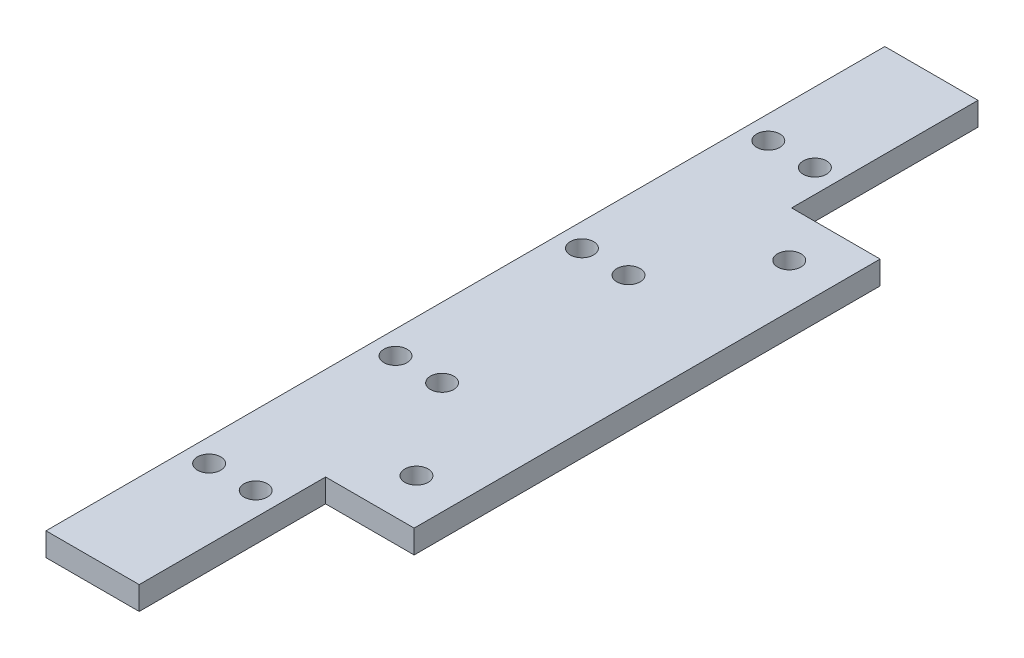
SolidWorks part; units mm, degrees
ref_plane "Front Plane" through (0, 0, 0) normal (0, 0, 1) x (1, 0, 0)
ref_plane "Top Plane" through (0, 0, 0) normal (0, 1, 0) x (1, 0, 0)
ref_plane "Right Plane" through (0, 0, 0) normal (1, 0, 0) x (0, 0, -1)
sketch "Sketch1" plane through (0, 0, 0) normal (0, 1, 0) x (1, 0, 0)
  line L1 (0, 0) -> (24.13, 0)
  line L2 (0, 0) -> (0, 127)
  line L3 (0, 127) -> (24.13, 127)
  line L4 (24.13, 0) -> (24.13, 127)
  dimension "D1" = 127
  dimension "D2" = 24.13
extrude "Boss-Extrude1" add sketch "Sketch1" along normal blind 6.35
sketch "Sketch3" plane through (0, 6.35, 0) normal (0, 1, 0) x (1, 0, 0)
  line L0 (12.065, 0) -> (12.065, 127)
  line L1 (0, 0) -> (24.13, 0) construction
  line L2 (24.13, 127) -> (0, 127) construction
  line L3 (12.065, 0) -> (12.065, 12.7)
  circle A0 centre (12.065, 12.7) radius 3.175
  circle A1 centre (12.065, 114.3) radius 3.175
  point P8 (12.065, 63.5)
  point P13 (12.065, 63.5)
  dimension "D2" = 6.35
  dimension "D1" = 12.7
  dimension "D3" = 2
extrude "Cut-Extrude2" cut sketch "Sketch3" against normal through all contours L0 A1 | L0 A1 | L3 A0 L0 | L0 A0 L3
sketch "Sketch5" plane through (0, 0, 0) normal (-1, 0, 0) x (0, 0, 1)
  line L1 (-127, 0) -> (0, 0)
  line L2 (-127, 0) -> (-127, 6.35)
  line L3 (-127, 6.35) -> (0, 6.35)
  line L4 (0, 0) -> (0, 6.35)
extrude "Boss-Extrude2" add sketch "Sketch5" along normal blind 25.4
sketch "Sketch6" plane through (0, 0, 0) normal (0, 0, 1) x (1, 0, 0)
  line L1 (-25.4, 6.35) -> (0, 6.35)
  line L2 (-25.4, 6.35) -> (-25.4, 0)
  line L3 (-25.4, 0) -> (0, 0)
  line L4 (0, 6.35) -> (0, 0)
extrude "Boss-Extrude3" add sketch "Sketch6" along normal blind 50.8
sketch "Sketch7" plane through (0, 0, -127) normal (0, 0, -1) x (-1, 0, 0)
  line L1 (25.4, 6.35) -> (0, 6.35)
  line L2 (25.4, 6.35) -> (25.4, 0)
  line L3 (25.4, 0) -> (0, 0)
  line L4 (0, 6.35) -> (0, 0)
extrude "Boss-Extrude4" add sketch "Sketch7" along normal blind 50.8
sketch "Sketch8" plane through (0, 6.35, 0) normal (0, 1, 0) x (1, 0, 0)
  line L0 (-12.7, 177.8) -> (-12.7, -50.8)
  line L1 (-25.4, 177.8) -> (0, 177.8) construction
  line L2 (0, -50.8) -> (-25.4, -50.8) construction
  line L4 (0, 177.8) -> (-12.7, 177.8)
  line L5 (0, 177.8) -> (0, 139.7)
  line L6 (0, 139.7) -> (-12.7, 139.7)
  line L7 (-12.7, 177.8) -> (-12.7, 139.7)
  circle A0 centre (-6.35, 139.7) radius 3.175
  circle A1 centre (-19.05, 139.7) radius 3.175
  circle A2 centre (-6.35, 88.9) radius 3.175
  circle A3 centre (-19.05, 88.9) radius 3.175
  circle A4 centre (-6.35, 38.1) radius 3.175
  circle A5 centre (-19.05, 38.1) radius 3.175
  circle A6 centre (-6.35, -12.7) radius 3.175
  circle A7 centre (-19.05, -12.7) radius 3.175
  dimension "D2" = 6.35
  dimension "D1" = 38.1
  dimension "D3" = 2
  dimension "D4" = 4
extrude "Cut-Extrude3" cut sketch "Sketch8" against normal through all contours L6 A0 | L6 A0 | A1 | A3 | A2 | A5 | A4 | A6 | A7
